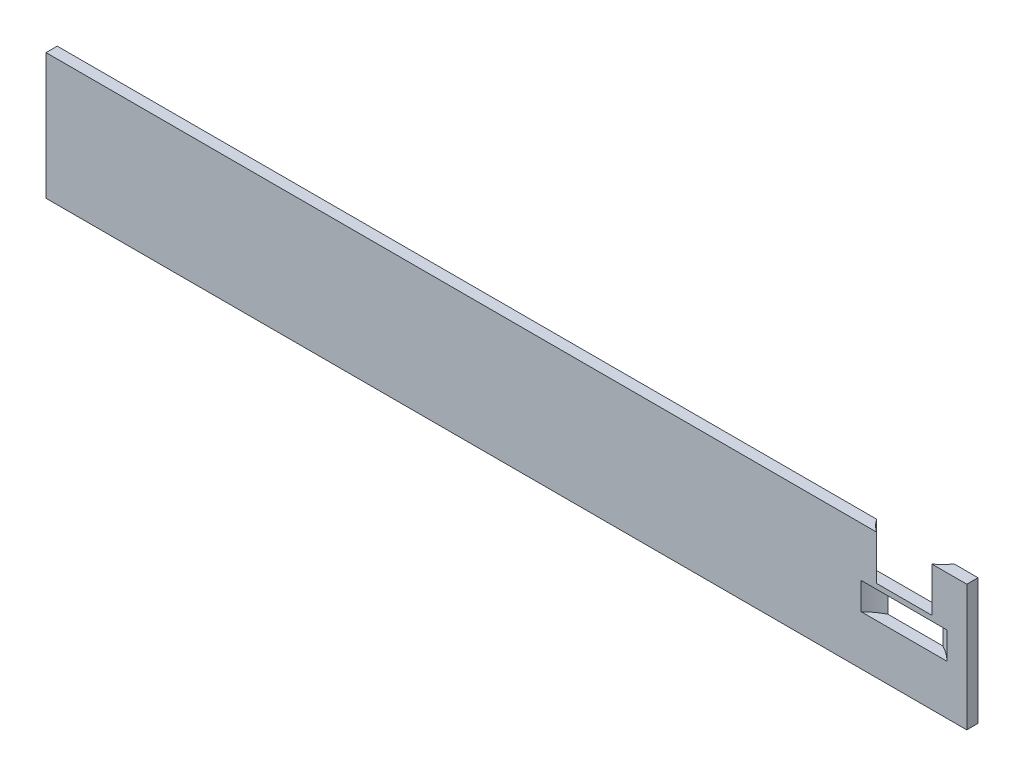
SolidWorks part; units mm, degrees
ref_plane "Alzado" through (0, 0, 0) normal (0, 0, 1) x (1, 0, 0)
ref_plane "Planta" through (0, 0, 0) normal (0, 1, 0) x (1, 0, 0)
ref_plane "Vista lateral" through (0, 0, 0) normal (1, 0, 0) x (0, 0, -1)
sketch "Croquis1" plane through (0, 0, 0) normal (0, 0, 1) x (1, 0, 0)
  line L1 (-985, 135) -> (0, 135)
  line L2 (-985, 135) -> (-985, 0)
  line L3 (-985, 0) -> (0, 0)
  line L4 (0, 135) -> (0, 0)
  dimension "D1" = 135
  dimension "D2" = 985
extrude "Saliente-Extruir1" add sketch "Croquis1" along normal blind 12
sketch "Croquis2" plane through (0, 135, 0) normal (0, 1, 0) x (1, 0, 0)
  line L0 (0, -12) -> (-985, -12) construction
  line L1 (-67, -12) -> (-67, 29) construction
  line L2 (-67, 29) -> (0, 29) construction
  line L3 (0, 29) -> (0, -12) construction
  line L4 (-25.5348, 0) -> (-108.4652, 0)
  line L5 (0, 0) -> (-985, 0) construction
  line L6 (-37.346, -12) -> (-96.654, -12)
  arc A0 (-108.4652, 0) -> (-96.654, -12) centre (-67, 29) ccw
  arc A1 (-37.346, -12) -> (-25.5348, 0) centre (-67, 29) ccw
  dimension "D3" = 101.2
  dimension "D1" = 41
  dimension "D2" = 67
extrude "Cortar-Extruir1" cut sketch "Croquis2" against normal blind 47.5
ref_plane "Plano1" through (0, 82, 0) normal (0, 1, 0) x (1, 0, 0)
sketch "Croquis3" plane through (0, 82, 0) normal (0, 1, 0) x (1, 0, 0)
  line L0 (-67, 0) -> (-67, -58) construction
  line L1 (-25.5348, 0) -> (-108.4652, 0) construction
  line L2 (-67, -58) -> (0, -58) construction
  line L3 (0, -58) -> (0, -12) construction
  circle A0 centre (-67, -58) radius 65
  dimension "D1" = 58
  dimension "D2" = 67
extrude "Cortar-Extruir2" cut sketch "Croquis3" against normal blind 29
